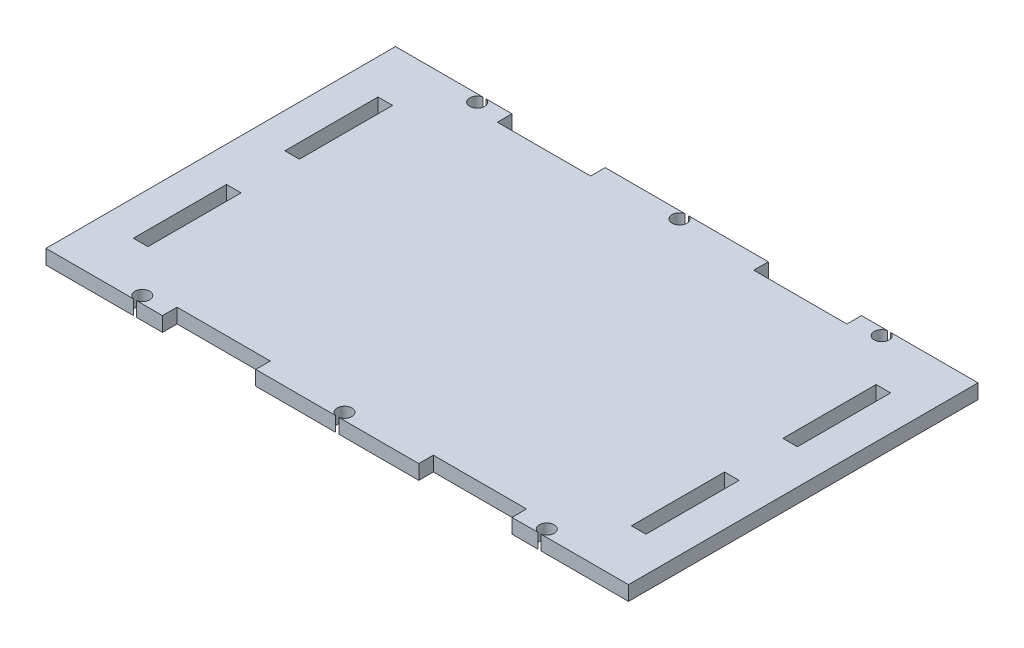
SolidWorks part; units mm, degrees
ref_plane "Front Plane" through (0, 0, 0) normal (0, 0, 1) x (1, 0, 0)
ref_plane "Top Plane" through (0, 0, 0) normal (0, 1, 0) x (1, 0, 0)
ref_plane "Right Plane" through (0, 0, 0) normal (1, 0, 0) x (0, 0, -1)
sketch "Sketch1" plane through (0, 0, 0) normal (0, 1, 0) x (1, 0, 0)
  line L1 (-63.5, 38.1) -> (63.5, 38.1)
  line L2 (-63.5, 38.1) -> (-63.5, -38.1)
  line L3 (-63.5, -38.1) -> (63.5, -38.1)
  line L4 (63.5, 38.1) -> (63.5, -38.1)
  line L5 (-63.5, 38.1) -> (63.5, -38.1) construction
  line L6 (-63.5, -38.1) -> (63.5, 38.1) construction
  point P0 (0, 0)
  point P5 (0, 0)
  dimension "D1" = 127
  dimension "D2" = 76.2
extrude "Boss-Extrude1" add sketch "Sketch1" along normal blind 3.175
sketch "Sketch2" plane through (0, 3.175, 0) normal (0, 1, 0) x (1, 0, 0)
  line L0 (63.5, 38.1) -> (-63.5, 38.1) construction
  line L1 (-55.88, 26.67) -> (-52.705, 26.67)
  line L2 (-55.88, 26.67) -> (-55.88, 6.35)
  line L3 (-55.88, 6.35) -> (-52.705, 6.35)
  line L4 (-52.705, 26.67) -> (-52.705, 6.35)
  line L5 (-55.88, 26.67) -> (-52.705, 6.35) construction
  line L6 (-55.88, 6.35) -> (-52.705, 26.67) construction
  line L7 (-52.705, -6.35) -> (-55.88, -6.35)
  line L8 (-52.705, -6.35) -> (-52.705, -26.67)
  line L9 (-52.705, -26.67) -> (-55.88, -26.67)
  line L10 (-55.88, -6.35) -> (-55.88, -26.67)
  line L11 (-52.705, -6.35) -> (-55.88, -26.67) construction
  line L12 (-52.705, -26.67) -> (-55.88, -6.35) construction
  line L13 (-63.5, -38.1) -> (63.5, -38.1) construction
  line L14 (-63.5, 38.1) -> (-63.5, -38.1) construction
  line L15 (0, 39.2758) -> (0, -43.7626) construction
  line L16 (52.705, -26.67) -> (55.88, -6.35) construction
  line L17 (52.705, -6.35) -> (55.88, -26.67) construction
  line L18 (55.88, 6.35) -> (52.705, 26.67) construction
  line L19 (55.88, 26.67) -> (52.705, 6.35) construction
  line L20 (55.88, -6.35) -> (55.88, -26.67)
  line L21 (52.705, -26.67) -> (55.88, -26.67)
  line L22 (52.705, -6.35) -> (52.705, -26.67)
  line L23 (52.705, -6.35) -> (55.88, -6.35)
  line L24 (52.705, 26.67) -> (52.705, 6.35)
  line L25 (55.88, 6.35) -> (52.705, 6.35)
  line L26 (55.88, 26.67) -> (55.88, 6.35)
  line L27 (55.88, 26.67) -> (52.705, 26.67)
  point P0 (-54.2925, 16.51)
  point P5 (-54.2925, -16.51)
  point P14 (-54.2925, -26.67)
  point P28 (54.2925, -16.51)
  point P29 (54.2925, 16.51)
  dimension "D1" = 3.175
  dimension "D2" = 12.7
  dimension "D3" = 11.43
  dimension "D4" = 11.43
  dimension "D5" = 7.62
extrude "Cut-Extrude1" cut sketch "Sketch2" against normal blind 3.175
sketch "Sketch3" plane through (0, 3.175, 0) normal (0, 1, 0) x (1, 0, 0)
  line L1 (-38.1, 38.1) -> (-17.78, 38.1)
  line L2 (-38.1, 38.1) -> (-38.1, 34.925)
  line L3 (-38.1, 34.925) -> (-17.78, 34.925)
  line L4 (-17.78, 38.1) -> (-17.78, 34.925)
  line L5 (-38.1, 38.1) -> (-17.78, 34.925) construction
  line L6 (-38.1, 34.925) -> (-17.78, 38.1) construction
  line L7 (63.5, 38.1) -> (-63.5, 38.1) construction
  line L8 (-63.5, 38.1) -> (-63.5, -38.1) construction
  line L9 (0, 44.2183) -> (0, -55.6268) construction
  line L10 (-68.1178, 0) -> (73.9469, 0) construction
  line L11 (38.1, 34.925) -> (17.78, 38.1) construction
  line L12 (38.1, 38.1) -> (17.78, 34.925) construction
  line L13 (17.78, 38.1) -> (17.78, 34.925)
  line L14 (38.1, 34.925) -> (17.78, 34.925)
  line L15 (38.1, 38.1) -> (38.1, 34.925)
  line L16 (38.1, 38.1) -> (17.78, 38.1)
  line L17 (38.1, -38.1) -> (17.78, -34.925) construction
  line L18 (38.1, -34.925) -> (17.78, -38.1) construction
  line L19 (-38.1, -34.925) -> (-17.78, -38.1) construction
  line L20 (-38.1, -38.1) -> (-17.78, -34.925) construction
  line L21 (38.1, -38.1) -> (17.78, -38.1)
  line L22 (38.1, -38.1) -> (38.1, -34.925)
  line L23 (38.1, -34.925) -> (17.78, -34.925)
  line L24 (17.78, -38.1) -> (17.78, -34.925)
  line L25 (-17.78, -38.1) -> (-17.78, -34.925)
  line L26 (-38.1, -34.925) -> (-17.78, -34.925)
  line L27 (-38.1, -38.1) -> (-38.1, -34.925)
  line L28 (-38.1, -38.1) -> (-17.78, -38.1)
  point P0 (-27.94, 36.5125)
  point P9 (-38.1, 36.5125)
  point P19 (27.94, 36.5125)
  point P28 (27.94, -36.5125)
  point P29 (-27.94, -36.5125)
  dimension "D1" = 25.4
  dimension "D2" = 20.32
  dimension "D3" = 3.175
extrude "Cut-Extrude2" cut sketch "Sketch3" against normal blind 3.175
sketch "Sketch4" plane through (0, 3.175, 0) normal (0, 1, 0) x (1, 0, 0)
  line L0 (0, 50.9935) -> (0, -46.9199) construction
  line L1 (-71.3604, 0) -> (80.917, 0) construction
  line L2 (-63.5, 38.1) -> (-63.5, -38.1) construction
  line L3 (63.5, 38.1) -> (38.1, 38.1) construction
  line L4 (-38.1, 38.1) -> (-63.5, 38.1) construction
  line L6 (17.78, 38.1) -> (-17.78, 38.1) construction
  line L7 (-63.5, 38.1) -> (-63.5, -38.1) construction
  circle A0 centre (-44.0944, 36.5125) radius 1.6256
  circle A1 centre (0, 36.5125) radius 1.6256
  circle A2 centre (44.0944, 36.5125) radius 1.6256
  circle A3 centre (44.0944, -36.5125) radius 1.6256
  circle A4 centre (0, -36.5125) radius 1.6256
  circle A5 centre (-44.0944, -36.5125) radius 1.6256
  point P24 (0, 0)
  dimension "D1" = 63.5
  dimension "D3" = 3.2512
  dimension "D4" = 3.2512
  dimension "D2" = 38.1
  dimension "D5" = 1.5875
  dimension "D6" = 1.5875
  dimension "D7" = 19.4056
extrude "Cut-Extrude3" cut sketch "Sketch4" against normal blind 3.175
